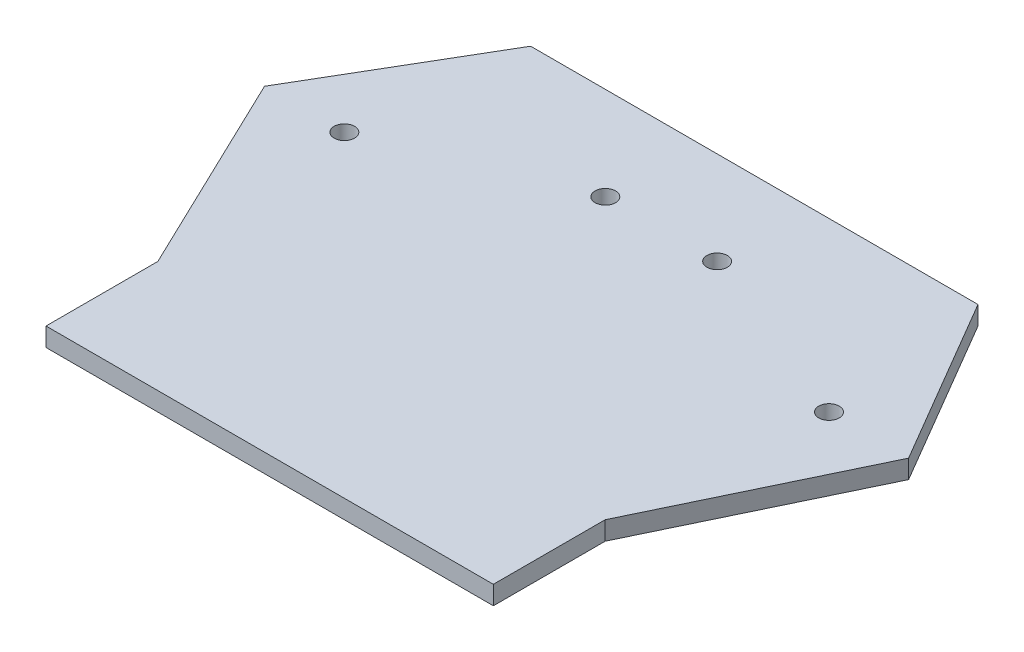
SolidWorks part; units mm, degrees
ref_plane "Front Plane" through (0, 0, 0) normal (0, 0, 1) x (1, 0, 0)
ref_plane "Top Plane" through (0, 0, 0) normal (0, 1, 0) x (1, 0, 0)
ref_plane "Right Plane" through (0, 0, 0) normal (1, 0, 0) x (0, 0, -1)
sketch "Sketch2" plane through (0, 0, 0) normal (0, 1, 0) x (1, 0, 0)
  line L0 (0, 0) -> (0, 29.9729)
  line L1 (60, 29.9729) -> (-60, 29.9729)
  line L2 (0, 29.9729) -> (0, 129.9729)
  line L3 (-60, 29.9729) -> (-60, -0.0271)
  line L5 (60, 129.9729) -> (-60, 129.9729)
  line L6 (-60, -0.0271) -> (60, -0.0271)
  line L7 (86.3843, 84.9729) -> (60, 29.9729)
  line L8 (86.3843, 84.9729) -> (60, 129.9729)
  line L9 (60, 29.9729) -> (60, -0.0271)
  line L10 (-86.3843, 84.9729) -> (-60, 129.9729)
  line L11 (-86.3843, 84.9729) -> (-60, 29.9729)
  line L12 (15, 105) -> (-15, 105)
  line L13 (-65, 85) -> (-15, 85)
  line L14 (-15, 85) -> (-15, 105)
  line L18 (-65, 85) -> (-32.5, 85)
  circle A0 centre (-15, 105) radius 2.75
  circle A1 centre (-65, 85) radius 2.75
  circle A2 centre (65, 85) radius 2.75
  circle A3 centre (15, 105) radius 2.75
  point P7 (0, 0)
  point P22 (0, -0.0271)
extrude "Boss-Extrude1" add sketch "Sketch2" along normal blind 5
